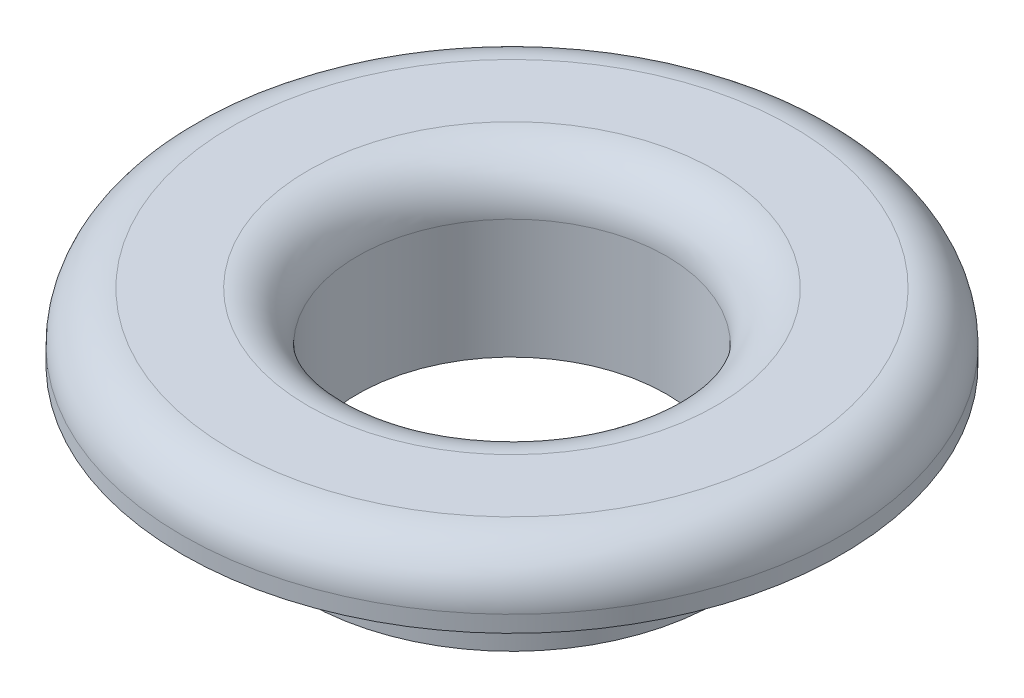
SolidWorks part; units mm, degrees
ref_plane "Front Plane" through (0, 0, 0) normal (0, 0, 1) x (1, 0, 0)
ref_plane "Top Plane" through (0, 0, 0) normal (0, 1, 0) x (1, 0, 0)
ref_plane "Right Plane" through (0, 0, 0) normal (1, 0, 0) x (0, 0, -1)
sketch "Sketch1" plane through (0, 0, 0) normal (0, 1, 0) x (1, 0, 0)
  circle A0 centre (0, 0) radius 2.3813
  circle A1 centre (0, 0) radius 3.175
  dimension "D1" = 4.7625
  dimension "D2" = 0.7937
extrude "Boss-Extrude1" add sketch "Sketch1" along normal blind 1.5875
sketch "Sketch2" plane through (0, 1.5875, 0) normal (0, 1, 0) x (1, 0, 0)
  circle A0 centre (0, 0) radius 5.08
  circle A1 centre (0, 0) radius 2.3813 construction
  circle A2 centre (0, 0) radius 2.3813
  dimension "D1" = 10.16
extrude "Boss-Extrude2" add sketch "Sketch2" along normal blind 1.016
fillet "Fillet1" radius 0.762 2 edges at (0, 2.6035, 5.08) (0, 2.6035, 2.3813)
ref_point "Point1"
